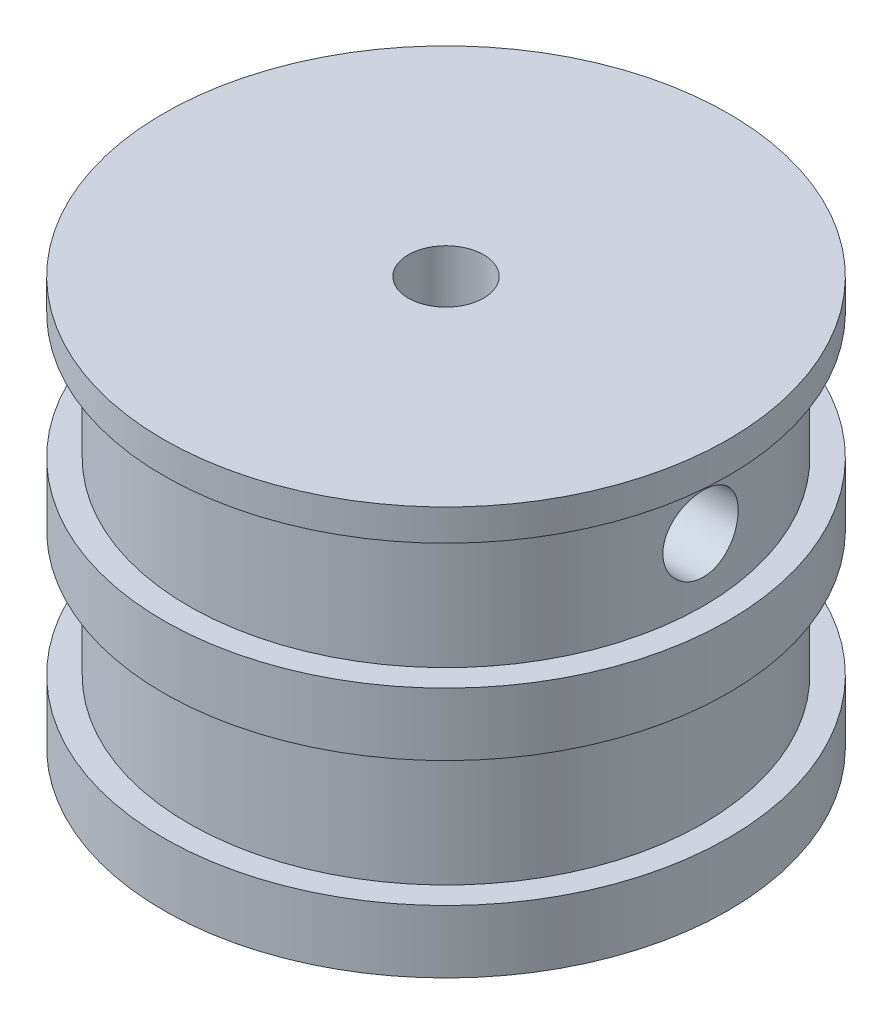
SolidWorks part; units mm, degrees
ref_plane "Front Plane" through (0, 0, 0) normal (0, 0, 1) x (1, 0, 0)
ref_plane "Top Plane" through (0, 0, 0) normal (0, 1, 0) x (1, 0, 0)
ref_plane "Right Plane" through (0, 0, 0) normal (1, 0, 0) x (0, 0, -1)
sketch "Sketch1" plane through (0, 0, 0) normal (0, 1, 0) x (1, 0, 0)
  circle A0 centre (0, 0) radius 22.5
  dimension "D1" = 45
extrude "Boss-Extrude1" add sketch "Sketch1" along normal blind 60 contours A0
sketch "Sketch2" plane through (0, 60, 0) normal (0, 1, 0) x (1, 0, 0)
  circle A0 centre (0, 0) radius 15
  dimension "D1" = 30
extrude "Cut-Extrude1" cut sketch "Sketch2" against normal blind 12
sketch "Sketch6" plane through (0, 0, 0) normal (0, 0, 1) x (1, 0, 0)
  line L0 (0, 0) -> (0, 60) construction
  line L1 (22.5, 60) -> (-22.5, 60) construction
  line L2 (0, 30) -> (-22.5, 30) construction
  line L3 (-22.5, 60) -> (-22.5, 0) construction
  line L4 (-22.5, 30) -> (-22.5, 60) construction
  line L5 (-22.5, 45) -> (0, 45) construction
  line L6 (-11.25, 45) -> (-11.25, 60) construction
  line L7 (15, 60) -> (-15, 60) construction
  line L8 (-11.25, 52.5) -> (-22.5, 52.5) construction
  line L9 (-22.5, 42.5) -> (-20.5, 42.5)
  line L10 (-22.5, 47.5) -> (-20.5, 47.5)
  line L12 (-22.5, 57.5) -> (-20.5, 57.5)
  line L13 (-20.5, 47.5) -> (-20.5, 57.5)
  line L14 (-22.5, 52.5) -> (-20.5, 57.5) construction
  line L15 (-22.5, 52.5) -> (-20.5, 47.5) construction
  line L16 (-20.5, 32.5) -> (-20.5, 42.5)
  line L17 (-22.5, 32.5) -> (-20.5, 32.5)
  line L18 (-22.5, 27.5) -> (-20.5, 27.5)
  line L19 (-20.5, 17.5) -> (-20.5, 27.5)
  line L20 (-22.5, 17.5) -> (-20.5, 17.5)
  line L21 (-22.5, 12.5) -> (-20.5, 12.5)
  line L22 (-20.5, 2.5) -> (-20.5, 12.5)
  line L23 (-22.5, 2.5) -> (-20.5, 2.5)
  line L24 (0, 0) -> (-22.5, 0) construction
  line L25 (-22.5, 57.5) -> (-22.5, 47.5)
  line L26 (-22.5, 42.5) -> (-22.5, 32.5)
  line L27 (-22.5, 27.5) -> (-22.5, 17.5)
  line L28 (-22.5, 12.5) -> (-22.5, 2.5)
  line L29 (-22.5, 57.5) -> (-22.5, 42.5) construction
  dimension "D1" = 10
  dimension "D2" = 2.5
  dimension "D3" = 2
  dimension "D5" = 2.5
  dimension "D7" = 15
  dimension "D4" = 4
  dimension "D6" = 4
revolve "Cut-Revolve1" cut sketch "Sketch6" angle 360 about L0
sketch "Sketch7" plane through (0, 0, 0) normal (0, -1, 0) x (1, 0, 0)
  circle A0 centre (0, 0) radius 22.5
  dimension "D1" = 45
extrude "Cut-Extrude2" cut sketch "Sketch7" against normal blind 27.5
sketch "Sketch8" plane through (0, 48, 0) normal (0, 1, 0) x (1, 0, 0)
  circle A0 centre (0, 0) radius 15
  dimension "D1" = 30
extrude "Cut-Extrude3" cut sketch "Sketch8" against normal blind 27.5
sketch "Sketch9" plane through (0, 0, 0) normal (1, 0, 0) x (0, 0, -1)
  line L0 (0, 0) -> (0, 60) construction
  line L1 (15, 60) -> (-15, 60) construction
  line L2 (-20.5, 52.5) -> (20.5, 52.5) construction
  line L3 (-20.5, 57.5) -> (-20.5, 47.5) construction
  line L4 (20.5, 47.5) -> (20.5, 57.5) construction
  circle A0 centre (0, 52.5) radius 2
  dimension "D1" = 4
extrude "Cut-Extrude5" cut sketch "Sketch9" against normal through all and the other way through all
sketch "Sketch10" plane through (0, 60, 0) normal (0, 1, 0) x (1, 0, 0)
  circle A0 centre (0, 0) radius 15
  dimension "D1" = 30
extrude "Boss-Extrude2" add sketch "Sketch10" against normal blind 32.5
sketch "Sketch11" plane through (0, 0, 0) normal (1, 0, 0) x (0, 0, -1)
  circle A0 centre (0, 52.5) radius 3
  dimension "D1" = 6
extrude "Cut-Extrude8" cut sketch "Sketch11" against normal through all and the other way through all
sketch "Sketch12" plane through (0, 60, 0) normal (0, 1, 0) x (1, 0, 0)
  circle A0 centre (0, 0) radius 3
  dimension "D1" = 6
extrude "Cut-Extrude9" cut sketch "Sketch12" against normal blind 32.5
